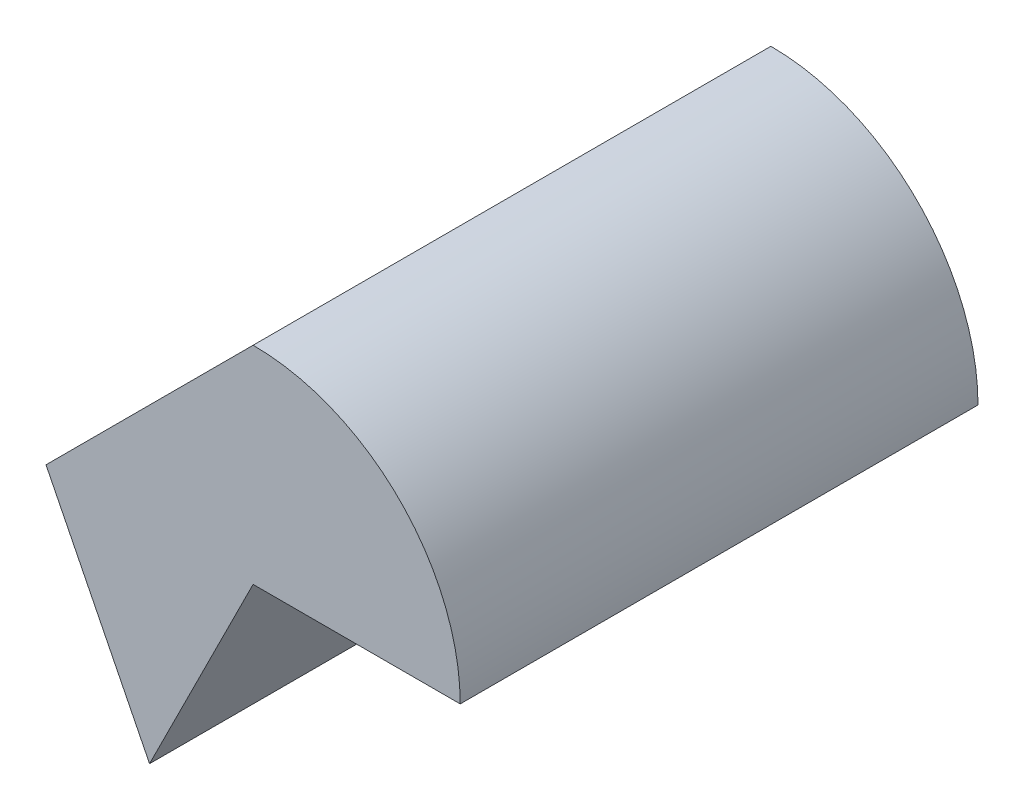
SolidWorks part; units mm, degrees
ref_plane "Front Plane" through (0, 0, 0) normal (0, 0, 1) x (1, 0, 0)
ref_plane "Top Plane" through (0, 0, 0) normal (0, 1, 0) x (1, 0, 0)
ref_plane "Right Plane" through (0, 0, 0) normal (1, 0, 0) x (0, 0, -1)
sketch "Sketch1" plane through (0, 0, 0) normal (0, 0, 1) x (1, 0, 0)
  line L0 (-10, 0) -> (0, 10)
  line L1 (0, 0) -> (10, 0)
  line L2 (0, 0) -> (-5, -10)
  line L3 (-5, -10) -> (-10, 0)
  arc A0 (0, 10) -> (10, 0) centre (0, 0) cw
  dimension "D1" = 10
  dimension "D2" = 10
  dimension "D3" = 10
  dimension "D4" = 10
  dimension "D5" = 10
  dimension "D6" = 5
extrude "Boss-Extrude1" add sketch "Sketch1" along normal blind 25
